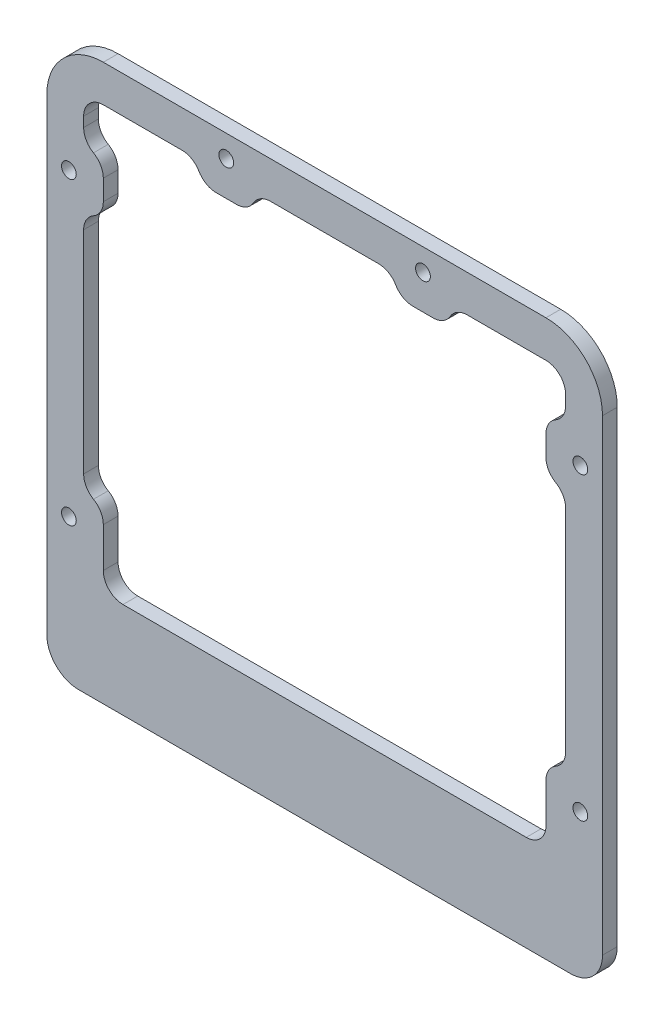
SolidWorks part; units mm, degrees
ref_plane "Front Plane" through (0, 0, 0) normal (0, 0, 1) x (1, 0, 0)
ref_plane "Top Plane" through (0, 0, 0) normal (0, 1, 0) x (1, 0, 0)
ref_plane "Right Plane" through (0, 0, 0) normal (1, 0, 0) x (0, 0, -1)
sketch "Sketch2" plane through (0, 0, -649.5896) normal (0, 0, 1) x (1, 0, 0)
  line L8 (40.9739, 223.8537) -> (-49.0261, 223.8537)
  line L9 (-60.5261, 212.3537) -> (-60.5261, 117.3537)
  line L10 (-54.0261, 110.8537) -> (45.9739, 110.8537)
  line L11 (52.4739, 117.3537) -> (52.4739, 212.3537)
  line L12 (40.9739, 223.8537) -> (-49.0261, 223.8537)
  line L13 (-60.5261, 212.3537) -> (-60.5261, 117.3537)
  line L14 (-54.0261, 110.8537) -> (45.9739, 110.8537)
  line L15 (52.4739, 117.3537) -> (52.4739, 212.3537)
  line L39 (-53.0261, 192.3537) -> (-53.0261, 162.3537)
  line L41 (-53.0261, 192.3537) -> (-53.0261, 162.3537)
  line L43 (-53.0261, 162.3537) -> (-53.0261, 149.3537)
  line L45 (-53.0261, 162.3537) -> (-53.0261, 149.3537)
  line L92 (-49.0261, 142.4255) -> (-49.0261, 134.3537)
  line L93 (-49.0261, 142.4255) -> (-49.0261, 134.3537)
  line L94 (-45.0261, 130.3537) -> (36.9739, 130.3537)
  line L95 (-45.0261, 130.3537) -> (36.9739, 130.3537)
  line L96 (40.9739, 134.3537) -> (40.9739, 142.4255)
  line L97 (40.9739, 134.3537) -> (40.9739, 142.4255)
  line L98 (44.9739, 149.3537) -> (44.9739, 192.3537)
  line L99 (44.9739, 149.3537) -> (44.9739, 192.3537)
  line L100 (40.9739, 199.2819) -> (40.9739, 203.4255)
  line L101 (40.9739, 199.2819) -> (40.9739, 203.4255)
  line L102 (44.9739, 210.3537) -> (44.9739, 212.3537)
  line L103 (44.9739, 210.3537) -> (44.9739, 212.3537)
  line L104 (40.9739, 216.3537) -> (24.9739, 216.3537)
  line L105 (40.9739, 216.3537) -> (24.9739, 216.3537)
  line L106 (18.0457, 212.3537) -> (13.9021, 212.3537)
  line L107 (18.0457, 212.3537) -> (13.9021, 212.3537)
  line L108 (6.9739, 216.3537) -> (-15.0261, 216.3537)
  line L109 (6.9739, 216.3537) -> (-15.0261, 216.3537)
  line L110 (-21.9543, 212.3537) -> (-26.0979, 212.3537)
  line L111 (-21.9543, 212.3537) -> (-26.0979, 212.3537)
  line L112 (-33.0261, 216.3537) -> (-49.0261, 216.3537)
  line L113 (-33.0261, 216.3537) -> (-49.0261, 216.3537)
  line L114 (-53.0261, 212.3537) -> (-53.0261, 210.3537)
  line L115 (-53.0261, 212.3537) -> (-53.0261, 210.3537)
  line L116 (-49.0261, 203.4255) -> (-49.0261, 199.2819)
  line L117 (-49.0261, 203.4255) -> (-49.0261, 199.2819)
  arc A8 (52.4739, 212.3537) -> (40.9739, 223.8537) centre (40.9739, 212.3537) ccw
  arc A9 (-49.0261, 223.8537) -> (-60.5261, 212.3537) centre (-49.0261, 212.3537) ccw
  arc A10 (-60.5261, 117.3537) -> (-54.0261, 110.8537) centre (-54.0261, 117.3537) ccw
  arc A11 (45.9739, 110.8537) -> (52.4739, 117.3537) centre (45.9739, 117.3537) ccw
  arc A12 (52.4739, 212.3537) -> (40.9739, 223.8537) centre (40.9739, 212.3537) ccw
  arc A13 (-49.0261, 223.8537) -> (-60.5261, 212.3537) centre (-49.0261, 212.3537) ccw
  arc A14 (-60.5261, 117.3537) -> (-54.0261, 110.8537) centre (-54.0261, 117.3537) ccw
  arc A15 (45.9739, 110.8537) -> (52.4739, 117.3537) centre (45.9739, 117.3537) ccw
  circle A38 centre (-56.0261, 201.3537) radius 1.5
  circle A39 centre (-56.0261, 201.3537) radius 1.5
  circle A41 centre (-24.0261, 219.3567) radius 1.5
  circle A42 centre (-24.0261, 219.3567) radius 1.5
  circle A44 centre (15.9739, 219.3567) radius 1.5
  circle A45 centre (15.9739, 219.3567) radius 1.5
  circle A47 centre (47.9739, 201.3537) radius 1.5
  circle A48 centre (47.9739, 201.3537) radius 1.5
  circle A50 centre (47.9739, 140.3537) radius 1.5
  circle A51 centre (47.9739, 140.3537) radius 1.5
  circle A53 centre (-56.0261, 140.3537) radius 1.5
  circle A54 centre (-56.0261, 140.3537) radius 1.5
  arc A60 (-51.0261, 195.8178) -> (-53.0261, 192.3537) centre (-49.0261, 192.3537) ccw
  arc A62 (-51.0261, 195.8178) -> (-53.0261, 192.3537) centre (-49.0261, 192.3537) ccw
  arc A64 (-53.0261, 149.3537) -> (-51.0261, 145.8896) centre (-49.0261, 149.3537) ccw
  arc A66 (-53.0261, 149.3537) -> (-51.0261, 145.8896) centre (-49.0261, 149.3537) ccw
  arc A146 (-49.0261, 142.4255) -> (-51.0261, 145.8896) centre (-53.0261, 142.4255) ccw
  arc A147 (-49.0261, 142.4255) -> (-51.0261, 145.8896) centre (-53.0261, 142.4255) ccw
  arc A148 (-49.0261, 134.3537) -> (-45.0261, 130.3537) centre (-45.0261, 134.3537) ccw
  arc A149 (-49.0261, 134.3537) -> (-45.0261, 130.3537) centre (-45.0261, 134.3537) ccw
  arc A150 (36.9739, 130.3537) -> (40.9739, 134.3537) centre (36.9739, 134.3537) ccw
  arc A151 (36.9739, 130.3537) -> (40.9739, 134.3537) centre (36.9739, 134.3537) ccw
  arc A152 (42.9739, 145.8896) -> (40.9739, 142.4255) centre (44.9739, 142.4255) ccw
  arc A153 (42.9739, 145.8896) -> (40.9739, 142.4255) centre (44.9739, 142.4255) ccw
  arc A154 (42.9739, 145.8896) -> (44.9739, 149.3537) centre (40.9739, 149.3537) ccw
  arc A155 (42.9739, 145.8896) -> (44.9739, 149.3537) centre (40.9739, 149.3537) ccw
  arc A156 (44.9739, 192.3537) -> (42.9739, 195.8178) centre (40.9739, 192.3537) ccw
  arc A157 (44.9739, 192.3537) -> (42.9739, 195.8178) centre (40.9739, 192.3537) ccw
  arc A158 (40.9739, 199.2819) -> (42.9739, 195.8178) centre (44.9739, 199.2819) ccw
  arc A159 (40.9739, 199.2819) -> (42.9739, 195.8178) centre (44.9739, 199.2819) ccw
  arc A160 (42.9739, 206.8896) -> (40.9739, 203.4255) centre (44.9739, 203.4255) ccw
  arc A161 (42.9739, 206.8896) -> (40.9739, 203.4255) centre (44.9739, 203.4255) ccw
  arc A162 (42.9739, 206.8896) -> (44.9739, 210.3537) centre (40.9739, 210.3537) ccw
  arc A163 (42.9739, 206.8896) -> (44.9739, 210.3537) centre (40.9739, 210.3537) ccw
  arc A164 (44.9739, 212.3537) -> (40.9739, 216.3537) centre (40.9739, 212.3537) ccw
  arc A165 (44.9739, 212.3537) -> (40.9739, 216.3537) centre (40.9739, 212.3537) ccw
  arc A166 (24.9739, 216.3537) -> (21.5098, 214.3537) centre (24.9739, 212.3537) ccw
  arc A167 (24.9739, 216.3537) -> (21.5098, 214.3537) centre (24.9739, 212.3537) ccw
  arc A168 (18.0457, 212.3537) -> (21.5098, 214.3537) centre (18.0457, 216.3537) ccw
  arc A169 (18.0457, 212.3537) -> (21.5098, 214.3537) centre (18.0457, 216.3537) ccw
  arc A170 (10.438, 214.3537) -> (13.9021, 212.3537) centre (13.9021, 216.3537) ccw
  arc A171 (10.438, 214.3537) -> (13.9021, 212.3537) centre (13.9021, 216.3537) ccw
  arc A172 (10.438, 214.3537) -> (6.9739, 216.3537) centre (6.9739, 212.3537) ccw
  arc A173 (10.438, 214.3537) -> (6.9739, 216.3537) centre (6.9739, 212.3537) ccw
  arc A174 (-15.0261, 216.3537) -> (-18.4902, 214.3537) centre (-15.0261, 212.3537) ccw
  arc A175 (-15.0261, 216.3537) -> (-18.4902, 214.3537) centre (-15.0261, 212.3537) ccw
  arc A176 (-21.9543, 212.3537) -> (-18.4902, 214.3537) centre (-21.9543, 216.3537) ccw
  arc A177 (-21.9543, 212.3537) -> (-18.4902, 214.3537) centre (-21.9543, 216.3537) ccw
  arc A178 (-29.562, 214.3537) -> (-26.0979, 212.3537) centre (-26.0979, 216.3537) ccw
  arc A179 (-29.562, 214.3537) -> (-26.0979, 212.3537) centre (-26.0979, 216.3537) ccw
  arc A180 (-29.562, 214.3537) -> (-33.0261, 216.3537) centre (-33.0261, 212.3537) ccw
  arc A181 (-29.562, 214.3537) -> (-33.0261, 216.3537) centre (-33.0261, 212.3537) ccw
  arc A182 (-49.0261, 216.3537) -> (-53.0261, 212.3537) centre (-49.0261, 212.3537) ccw
  arc A183 (-49.0261, 216.3537) -> (-53.0261, 212.3537) centre (-49.0261, 212.3537) ccw
  arc A184 (-53.0261, 210.3537) -> (-51.0261, 206.8896) centre (-49.0261, 210.3537) ccw
  arc A185 (-53.0261, 210.3537) -> (-51.0261, 206.8896) centre (-49.0261, 210.3537) ccw
  arc A186 (-49.0261, 203.4255) -> (-51.0261, 206.8896) centre (-53.0261, 203.4255) ccw
  arc A187 (-49.0261, 203.4255) -> (-51.0261, 206.8896) centre (-53.0261, 203.4255) ccw
  arc A188 (-51.0261, 195.8178) -> (-49.0261, 199.2819) centre (-53.0261, 199.2819) ccw
  arc A189 (-51.0261, 195.8178) -> (-49.0261, 199.2819) centre (-53.0261, 199.2819) ccw
  dimension "D1" = 1.5
  dimension "D2" = 2
  dimension "D3" = 0
  dimension "D4" = 0
  dimension "D5" = 0
  dimension "D6" = 0
  dimension "D7" = 0
  dimension "D8" = 0
extrude "Boss-Extrude4" add sketch "Sketch2" along normal blind 3
